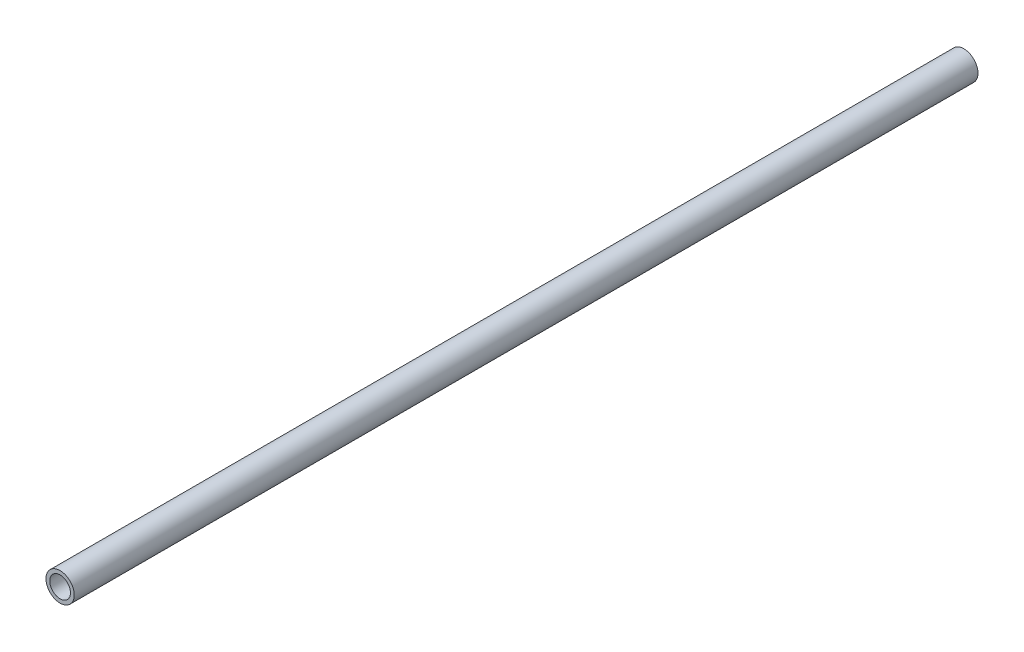
SolidWorks part; units mm, degrees
ref_plane "Front Plane" through (0, 0, 0) normal (0, 0, 1) x (1, 0, 0)
ref_plane "Top Plane" through (0, 0, 0) normal (0, 1, 0) x (1, 0, 0)
ref_plane "Right Plane" through (0, 0, 0) normal (1, 0, 0) x (0, 0, -1)
sketch "Sketch1" plane through (0, 0, 0) normal (0, 0, 1) x (1, 0, 0)
  circle A0 centre (0, 0) radius 9.525
  circle A1 centre (0, 0) radius 6.985
  dimension "D1" = 19.05
  dimension "D2" = 2.54
extrude "Boss-Extrude1" add sketch "Sketch1" along normal blind 609.6
